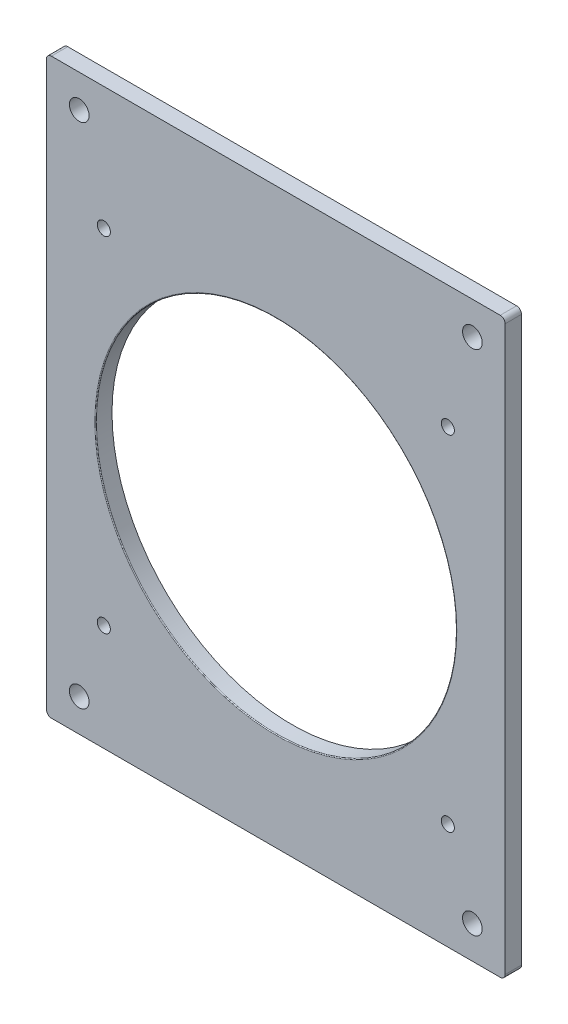
SolidWorks part; units mm, degrees
material "Alliage 1060"
ref_plane "Plan de face" through (0, 0, 0) normal (0, 0, 1) x (1, 0, 0)
ref_plane "Plan de dessus" through (0, 0, 0) normal (0, 1, 0) x (1, 0, 0)
ref_plane "Plan de droite" through (0, 0, 0) normal (1, 0, 0) x (0, 0, -1)
sketch "Esquisse1" plane through (0, 0, 0) normal (0, 0, 1) x (1, 0, 0)
  line L0 (-68, 87.5) -> (-68.5, 87.5)
  line L1 (-68, -87.5) -> (68, -87.5)
  line L2 (-70, -85.5) -> (-70, 75.5)
  line L3 (-68, 87.5) -> (68, 87.5)
  line L4 (70, -85.5) -> (70, 75.5)
  line L5 (-70, -87.5) -> (70, 87.5) construction
  line L6 (-70, 87.5) -> (70, -87.5) construction
  line L7 (-70, 86) -> (-70, 75.5)
  line L8 (68, 87.5) -> (68.5, 87.5)
  line L9 (70, 86) -> (70, 75.5)
  line L10 (68, -87.5) -> (68.5, -87.5)
  line L11 (70, -86) -> (70, -85.5)
  line L12 (-68, -87.5) -> (-68.5, -87.5)
  line L13 (-70, -86) -> (-70, -85.5)
  arc A4 (-68.5, 87.5) -> (-70, 86) centre (-68.5, 86) ccw
  arc A5 (68.5, 87.5) -> (70, 86) centre (68.5, 86) cw
  arc A6 (68.5, -87.5) -> (70, -86) centre (68.5, -86) ccw
  arc A7 (-68.5, -87.5) -> (-70, -86) centre (-68.5, -86) cw
  point P0 (0, 0)
  dimension "D3" = 1.5
  dimension "D4" = 1.5
  dimension "D1" = 175
  dimension "D2" = 140
extrude "Boss.-Extru.1" add sketch "Esquisse1" along normal blind 5
ref_plane "PlanSagital" through (0, 0, 0) normal (1, 0, 0) x (0, 0, -1)
ref_plane "Plan2" through (0, -62.5, 0) normal (0, -1, 0) x (-1, 0, 0)
sketch "Esquisse4" plane through (0, 0, 5) normal (0, 0, 1) x (1, 0, 0)
  circle A0 centre (-60, -77.5) radius 3
  circle A1 centre (60, -77.5) radius 3
  circle A2 centre (-60, 77.5) radius 3
  circle A3 centre (60, 77.5) radius 3
extrude "Enlèv. mat.-Extru.3" cut sketch "Esquisse4" against normal blind 10
sketch "Esquisse5" plane through (0, 0, 0) normal (0, 0, -1) x (-1, 0, 0)
  circle A0 centre (-52.5, 50) radius 2
  circle A1 centre (52.5, 50) radius 2
  circle A2 centre (52.5, -55) radius 2
  circle A3 centre (-52.5, -55) radius 2
  circle A4 centre (0, -2.5) radius 55
extrude "Enlèv. mat.-Extru.4" cut sketch "Esquisse5" against normal blind 10
fillet "Congé1" radius 0.25 1 edges at (-55, -2.5, 5)
